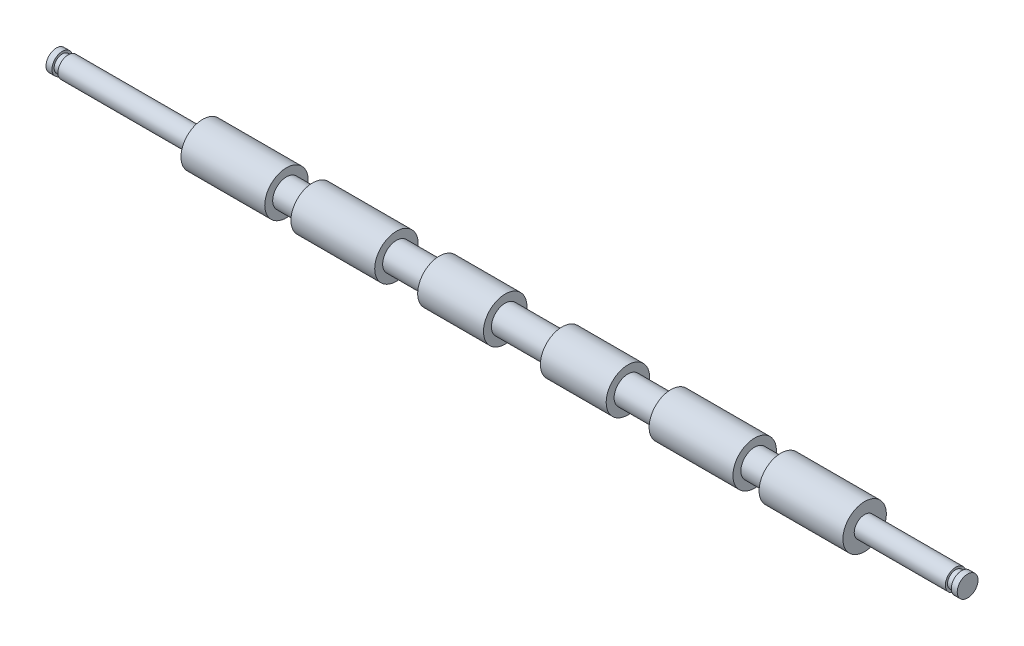
SolidWorks part; units mm, degrees
ref_plane "Face" through (0, 0, 0) normal (0, 0, 1) x (1, 0, 0)
ref_plane "Dessus" through (0, 0, 0) normal (0, 1, 0) x (1, 0, 0)
ref_plane "Droite" through (0, 0, 0) normal (1, 0, 0) x (0, 0, -1)
sketch "Esquisse1" plane through (0, 0, 0) normal (0, 0, 1) x (1, 0, 0)
  line L0 (0, 0) -> (273.4, 0) construction
  line L1 (0, 0) -> (0, 2.98)
  line L2 (0, 2.98) -> (1.7, 2.98)
  line L3 (1.7, 2.98) -> (1.7, 2.35)
  line L4 (1.7, 2.35) -> (3.4, 2.35)
  line L5 (3.4, 2.35) -> (3.4, 2.98)
  line L6 (3.4, 2.98) -> (41.9, 2.98)
  line L7 (41.9, 2.98) -> (41.9, 6.225)
  line L8 (41.9, 6.225) -> (65.9, 6.225)
  line L9 (65.9, 6.225) -> (65.9, 3.95)
  line L10 (65.9, 3.95) -> (73.4, 3.95)
  line L11 (73.4, 3.95) -> (73.4, 6.225)
  line L12 (73.4, 6.225) -> (97.4, 6.225)
  line L13 (97.4, 6.225) -> (97.4, 3.95)
  line L14 (97.4, 3.95) -> (109.7, 3.95)
  line L15 (109.7, 3.95) -> (109.7, 6.225)
  line L16 (109.7, 6.225) -> (128.55, 6.225)
  line L17 (136.7, 0) -> (136.7, 3.95) construction
  line L18 (128.55, 6.225) -> (128.55, 3.95)
  line L19 (128.55, 3.95) -> (144.85, 3.95)
  line L20 (231.5, 2.98) -> (231.5, 6.225)
  line L21 (231.5, 6.225) -> (207.5, 6.225)
  line L22 (207.5, 3.95) -> (200, 3.95)
  line L23 (200, 3.95) -> (200, 6.225)
  line L24 (200, 6.225) -> (176, 6.225)
  line L25 (176, 6.225) -> (176, 3.95)
  line L26 (176, 3.95) -> (163.7, 3.95)
  line L27 (163.7, 3.95) -> (163.7, 6.225)
  line L28 (163.7, 6.225) -> (144.85, 6.225)
  line L29 (144.85, 6.225) -> (144.85, 3.95)
  line L30 (207.5, 6.225) -> (207.5, 3.95)
  line L31 (231.5, 2.98) -> (257.6, 2.98)
  line L32 (257.6, 2.98) -> (257.6, 2.35)
  line L33 (257.6, 2.35) -> (259.3, 2.35)
  line L34 (259.3, 2.35) -> (259.3, 2.98)
  line L35 (259.3, 2.98) -> (261, 2.98)
  line L36 (261, 2.98) -> (261, 0)
  line L37 (0, 0) -> (261, 0)
  dimension "D1" = 12.45
  dimension "D2" = 8.15
  dimension "D3" = 18.85
  dimension "D4" = 12.3
  dimension "D5" = 7.5
  dimension "D6" = 24
  dimension "D7" = 38.5
  dimension "D8" = 1.7
  dimension "D9" = 1.7
  dimension "D10" = 4.7
  dimension "D11" = 5.96
  dimension "D12" = 7.9
  dimension "D13" = 1.7
  dimension "D14" = 1.7
  dimension "D15" = 26.1
revolve "Révolution1" add sketch "Esquisse1" angle 360 about L37
ref_plane "Plan1" through (136.7, 0, 0) normal (-1, 0, 0) x (0, 0, 1)
ref_plane "Plan Milieux Axe" through (130.5, 0, 0) normal (-1, 0, 0) x (0, 0, 1)
